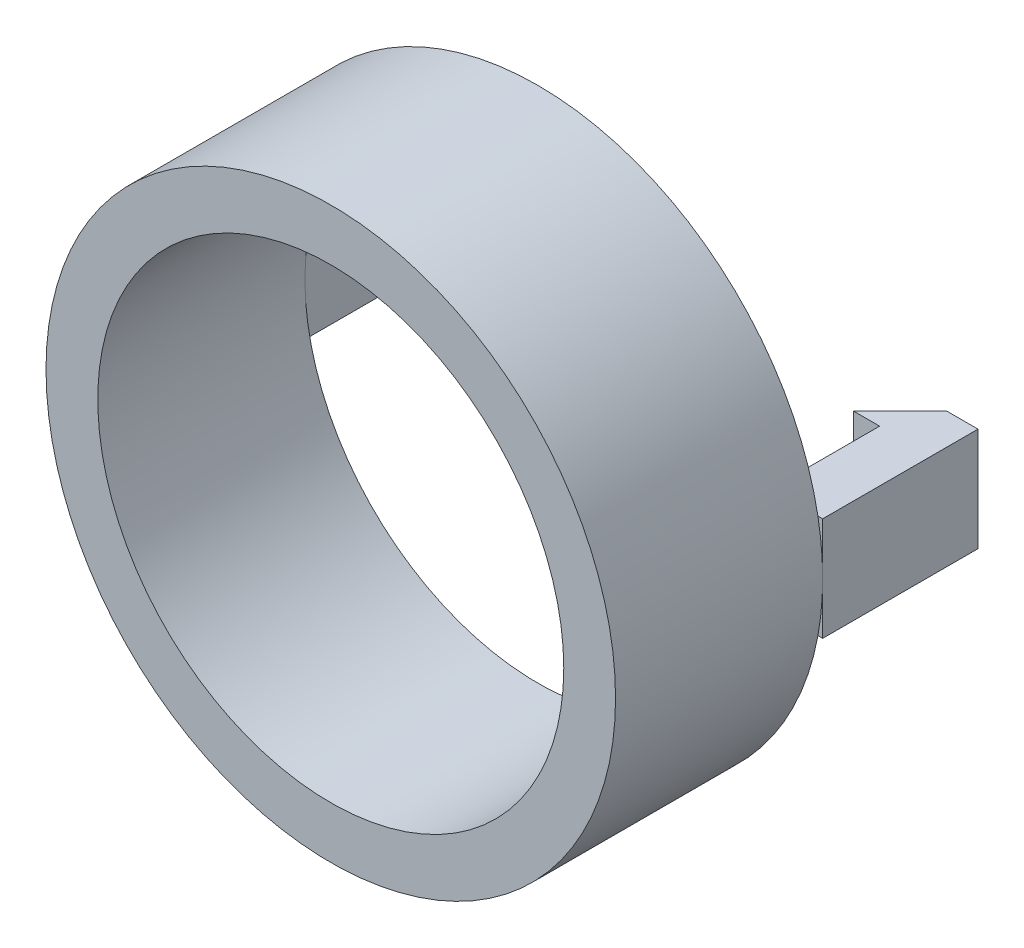
SolidWorks part; units mm, degrees
ref_plane "Front Plane" through (0, 0, 0) normal (0, 0, 1) x (1, 0, 0)
ref_plane "Top Plane" through (0, 0, 0) normal (0, 1, 0) x (1, 0, 0)
ref_plane "Right Plane" through (0, 0, 0) normal (1, 0, 0) x (0, 0, -1)
sketch "Sketch1" plane through (0, 0, 0) normal (0, 0, 1) x (1, 0, 0)
  circle A0 centre (0, 0) radius 9
  circle A1 centre (0, 0) radius 11
  dimension "D1" = 18
  dimension "D2" = 22
extrude "Boss-Extrude1" add sketch "Sketch1" along normal blind 8
sketch "Sketch2" plane through (0, 0, 0) normal (0, 1, 0) x (1, 0, 0)
  line L0 (-11, 0) -> (-11, 6)
  line L1 (-11, 6) -> (-9.8, 6)
  line L2 (-9.8, 6) -> (-8, 4.2)
  line L3 (-8, 4.2) -> (-9, 4.2)
  line L4 (-9, 4.2) -> (-9, 0)
  line L5 (9, 0) -> (-9, 0) construction
  line L6 (-9, 0) -> (-11, 0)
  line L7 (0, -4.4) -> (0, 4.4) construction
  line L8 (9, 0) -> (11, 0)
  line L9 (9, 4.2) -> (9, 0)
  line L10 (8, 4.2) -> (9, 4.2)
  line L11 (9.8, 6) -> (8, 4.2)
  line L12 (11, 6) -> (9.8, 6)
  line L13 (11, 0) -> (11, 6)
  dimension "D1" = 2
  dimension "D2" = 45
  dimension "D3" = 4.2
  dimension "D4" = 6
  dimension "D5" = 1
extrude "Boss-Extrude2" add sketch "Sketch2" along normal mid plane 4
